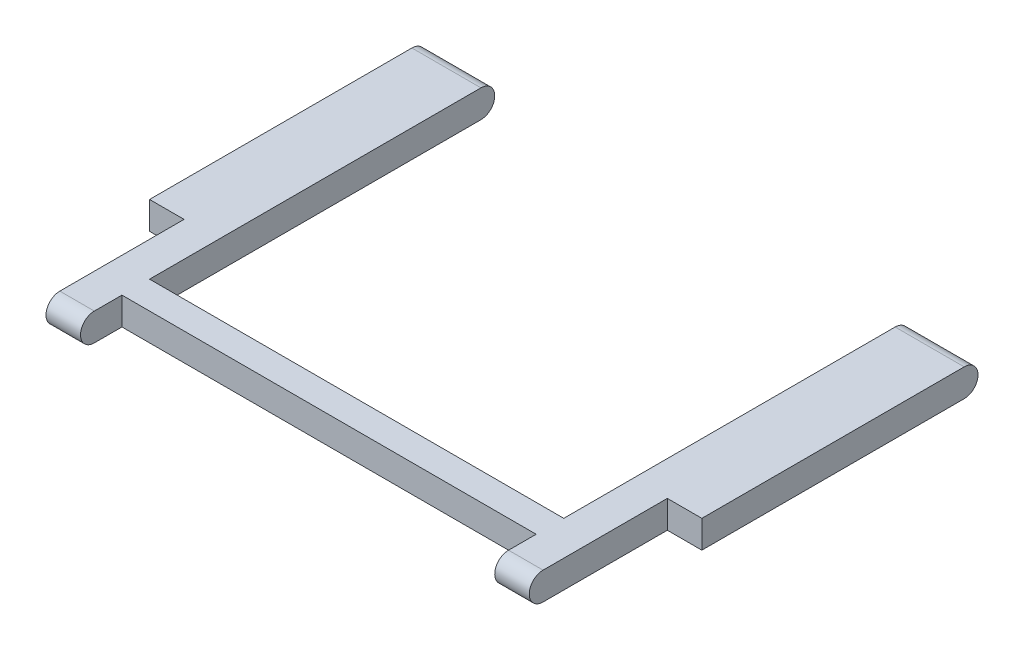
SolidWorks part; units mm, degrees
ref_plane "Front" through (0, 0, 0) normal (0, 0, 1) x (1, 0, 0)
ref_plane "Top" through (0, 0, 0) normal (0, 1, 0) x (1, 0, 0)
ref_plane "Right" through (0, 0, 0) normal (1, 0, 0) x (0, 0, -1)
sketch "草图2" plane through (0, 0, 0) normal (1, 0, 0) x (0, 0, -1)
  line L0 (-28, 0) -> (28, 0) construction
  line L1 (-28, 2) -> (28, 2)
  line L2 (-28, -2) -> (28, -2)
  arc A0 (-28, 2) -> (-28, -2) centre (-28, 0) ccw
  arc A1 (28, -2) -> (28, 2) centre (28, 0) ccw
  point P2 (0, 0)
extrude "凸台-拉伸1" add sketch "草图2" along normal blind 80
sketch "草图3" plane through (0, 2, 0) normal (0, 1, 0) x (1, 0, 0)
  line L0 (40, 30) -> (40, -34.3511) construction
  line L1 (80, 30) -> (0, 30) construction
  line L2 (80, -28) -> (0, -28) construction
  line L3 (10, -40.055) -> (70, -40.055)
  line L4 (10, -40.055) -> (10, -24)
  line L5 (10, -24) -> (70, -24)
  line L6 (70, -40.055) -> (70, -24)
  line L8 (10, 36.9603) -> (70, 36.9603)
  line L9 (10, 36.9603) -> (10, -20)
  line L10 (10, -20) -> (70, -20)
  line L11 (70, 36.9603) -> (70, -20)
  dimension "D1" = 60
  dimension "D2" = 30
  dimension "D3" = 4
  dimension "D4" = 4
  dimension "D5" = 30
  dimension "D6" = 30
extrude "切除-拉伸1" cut sketch "草图3" against normal blind 10
sketch "草图4" plane through (0, 2, 0) normal (0, 1, 0) x (1, 0, 0)
  line L0 (80, -30) -> (80, -28) construction
  line L1 (0, -30) -> (5, -30)
  line L2 (0, -30) -> (0, -10)
  line L3 (0, -10) -> (5, -10)
  line L4 (5, -30) -> (5, -10)
  line L5 (80, -30) -> (75, -30)
  line L6 (80, -30) -> (80, -10)
  line L7 (80, -10) -> (75, -10)
  line L8 (75, -30) -> (75, -10)
  dimension "D1" = 20
  dimension "D2" = 5
  dimension "D3" = 5
  dimension "D4" = 20
extrude "切除-拉伸2" cut sketch "草图4" against normal blind 10
